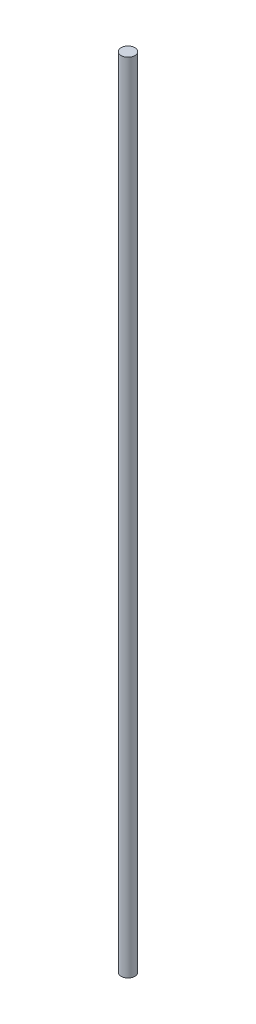
SolidWorks part; units mm, degrees
material "Plain Carbon Steel"
ref_plane "Front Plane" through (0, 0, 0) normal (0, 0, 1) x (1, 0, 0)
ref_plane "Top Plane" through (0, 0, 0) normal (0, 1, 0) x (1, 0, 0)
ref_plane "Right Plane" through (0, 0, 0) normal (1, 0, 0) x (0, 0, -1)
sketch "Sketch1" plane through (0, 0, 0) normal (0, 1, 0) x (1, 0, 0)
  circle A0 centre (0, 0) radius 3
extrude "Boss-Extrude1" add sketch "Sketch1" along normal blind 347.2
